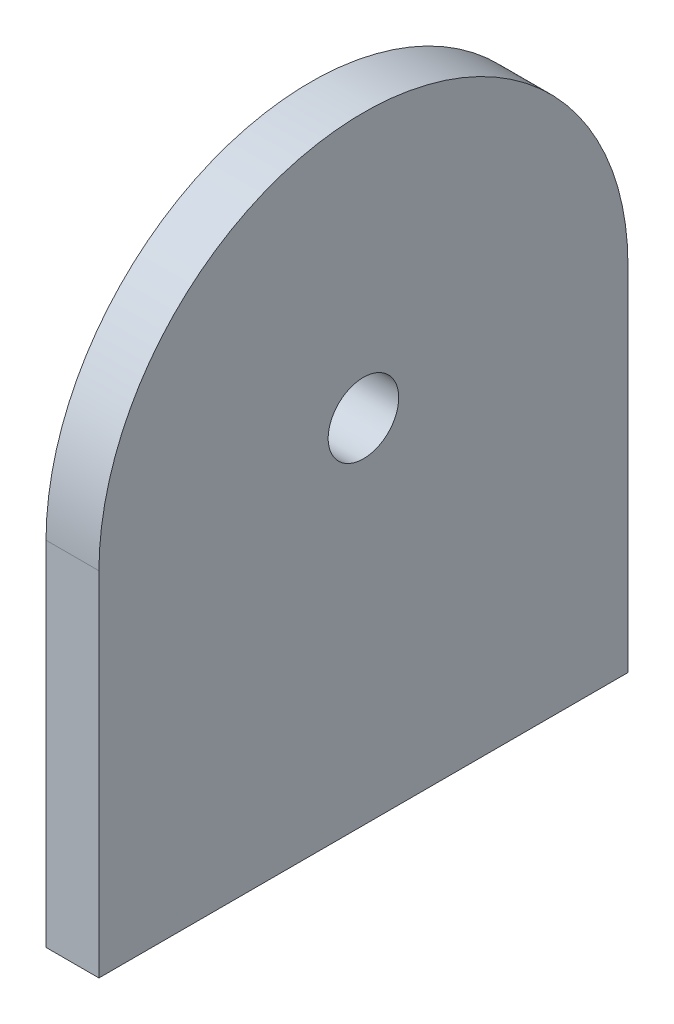
SolidWorks part; units mm, degrees
ref_plane "Alzado" through (0, 0, 0) normal (0, 0, 1) x (1, 0, 0)
ref_plane "Planta" through (0, 0, 0) normal (0, 1, 0) x (1, 0, 0)
ref_plane "Vista lateral" through (0, 0, 0) normal (1, 0, 0) x (0, 0, -1)
sketch "Croquis1" plane through (0, 0, 0) normal (1, 0, 0) x (0, 0, -1)
  line L0 (0, 20) -> (0, 0)
  line L1 (0, 0) -> (-30, 0)
  line L2 (-30, 0) -> (-30, 20)
  arc A0 (0, 20) -> (-30, 20) centre (-15, 20) ccw
  circle A1 centre (-15, 20) radius 2
  dimension "D3" = 4
  dimension "D4" = 15
  dimension "D1" = 30
  dimension "D2" = 20
  dimension "D5" = 20
extrude "Saliente-Extruir1" add sketch "Croquis1" along normal blind 3
